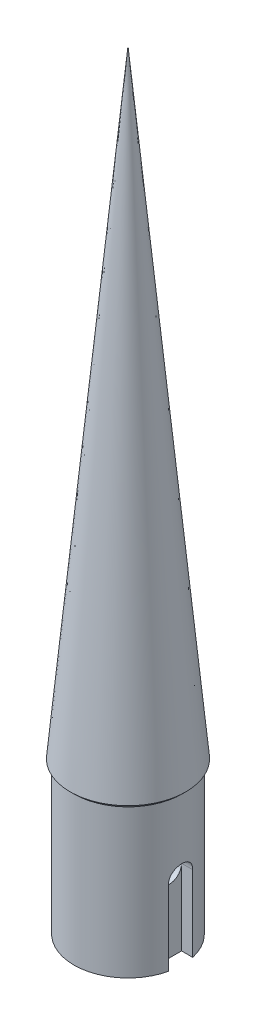
SolidWorks part; units mm, degrees
ref_plane "Front Plane" through (0, 0, 0) normal (0, 0, 1) x (1, 0, 0)
ref_plane "Top Plane" through (0, 0, 0) normal (0, 1, 0) x (1, 0, 0)
ref_plane "Right Plane" through (0, 0, 0) normal (1, 0, 0) x (0, 0, -1)
sketch "Sketch1" plane through (0, 0, 0) normal (0, 1, 0) x (1, 0, 0)
  circle A0 centre (0, 0) radius 8.895
  dimension "D1" = 17.79
extrude "Boss-Extrude1" add sketch "Sketch1" against normal blind 25
sketch "Sketch2" plane through (0, -25, 0) normal (0, -1, 0) x (1, 0, 0)
  line L0 (-6.8312, 1.9844) -> (-6.8312, -1.9844)
  line L1 (-6.8312, 1.9844) -> (-8.6708, 1.9844)
  line L2 (-6.8312, -1.9844) -> (-8.6708, -1.9844)
  line L3 (-8.895, 0) -> (-8.895, -1.1975) construction
  circle A0 centre (0, 0) radius 8.895 construction
  arc A1 (-8.6708, 1.9844) -> (-8.6708, -1.9844) centre (0, 0) ccw
  point P3 (-6.8313, 0)
  dimension "D2" = 3.9688
  dimension "D1" = 2.0637
extrude "Cut-Extrude1" cut sketch "Sketch2" against normal blind 12.5
mirror "Mirror1" about plane through (0, 0, 0) normal (1, 0, 0) of "Cut-Extrude1"
sketch "Sketch3" plane through (0, 0, 0) normal (1, 0, 0) x (0, 0, -1)
  line L0 (1.9844, -12.5) -> (-1.9844, -12.5) construction
  circle A0 centre (0, -12.5) radius 1.9844
extrude "Cut-Extrude2" cut sketch "Sketch3" against normal through all both and the other way through all
sketch "Sketch4" plane through (0, 0, 0) normal (0, 0, 1) x (1, 0, 0)
  line L0 (0, 0) -> (9.5, 0)
  line L1 (9.5, 0) -> (0, 101.6)
  line L2 (0, 101.6) -> (0, 0)
  dimension "D1" = 9.5
  dimension "D2" = 101.6
revolve "Revolve1" add sketch "Sketch4" angle 360 about L2
chamfer "Chamfer1" distance 0.6 angle 45 1 edges at (0, 0, 8.895)
equation "\"D_SHOULDER\"= 17.79mm"
equation "\"OD_AIRF\"= 19mm"
equation "\"W_CORD\"= 3.175mm"
equation "\"L_SHOULDER\"= 25mm"
equation "\"L_CONE\"= 4in"
equation "\"D1@Sketch1\"=\"D_SHOULDER\""
equation "\"D1@Boss-Extrude1\"=\"L_SHOULDER\""
equation "\"D2@Sketch2\"=1.25*\"W_CORD\""
equation "\"D1@Sketch2\"=0.65*\"W_CORD\""
equation "\"D1@Cut-Extrude1\"=\"L_SHOULDER\"/2"
equation "\"D1@Sketch4\"=0.5*\"OD_AIRF\""
equation "\"D2@Sketch4\"=\"L_CONE\""
